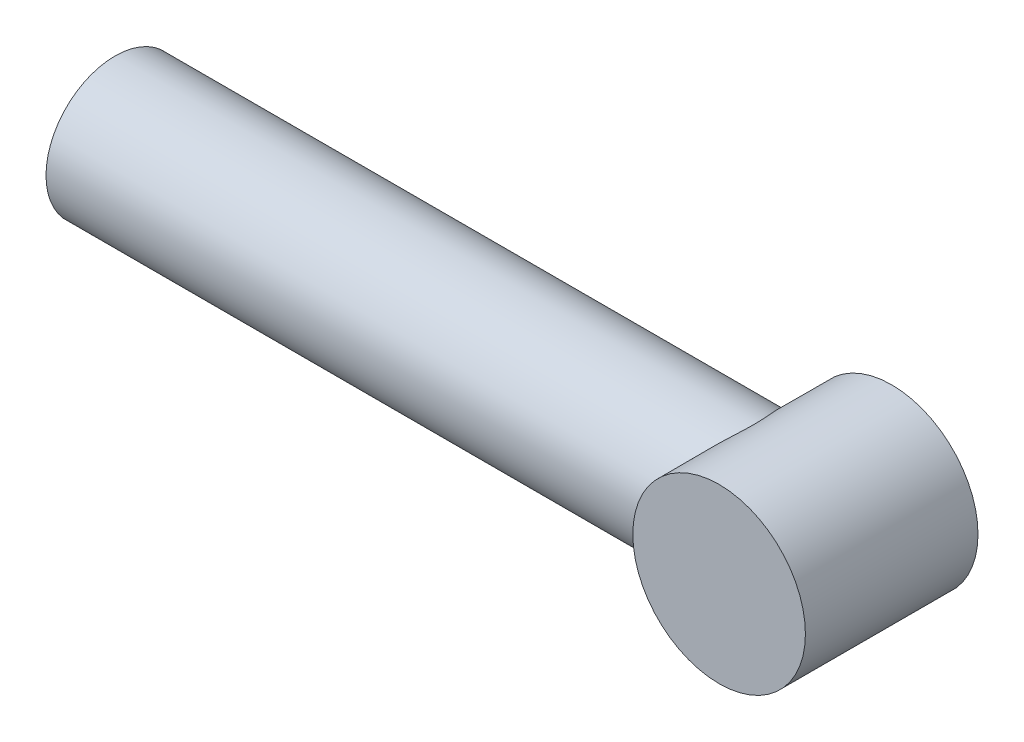
SolidWorks part; units mm, degrees
ref_plane "前视基准面" through (0, 0, 0) normal (0, 0, 1) x (1, 0, 0)
ref_plane "上视基准面" through (0, 0, 0) normal (0, 1, 0) x (1, 0, 0)
ref_plane "右视基准面" through (0, 0, 0) normal (1, 0, 0) x (0, 0, -1)
sketch "草图1" plane through (0, 0, 0) normal (1, 0, 0) x (0, 0, -1)
  circle A0 centre (0, 0) radius 40
extrude "凸台-拉伸1" add sketch "草图1" along normal mid plane 400
sketch "草图2" plane through (0, 0, 0) normal (0, 0, 1) x (1, 0, 0)
  line L0 (200, -40) -> (200, 40) construction
  circle A0 centre (200, 0) radius 50
extrude "凸台-拉伸2" add sketch "草图2" along normal mid plane 100
